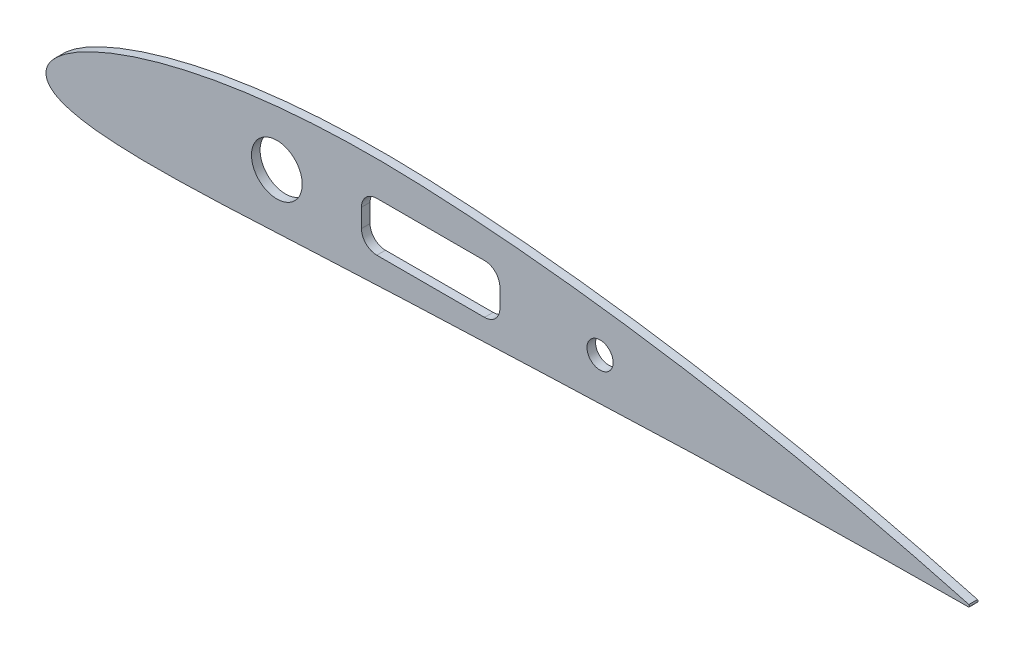
SolidWorks part; units mm, degrees
material "Фанера"
ref_plane "Front Plane" through (0, 0, 0) normal (0, 0, 1) x (1, 0, 0)
ref_plane "Top Plane" through (0, 0, 0) normal (0, 1, 0) x (1, 0, 0)
ref_plane "Right Plane" through (0, 0, 0) normal (1, 0, 0) x (0, 0, -1)
curve "Кривая3"
  spline degree 3 poles (0.0025, -0.1472, 0) (0.0289, -0.4455, 0) (0.0833, -1.0612, 0) (0.4227, -1.9666, 0) (0.9763, -2.8381, 0) (1.7565, -3.6471, 0) (2.7491, -4.3932, 0) (3.9671, -5.0829, 0) (5.4423, -5.7284, 0) (7.2357, -6.3386, 0) (9.4428, -6.9184, 0) (12.2026, -7.4661, 0) (15.6905, -7.9675, 0) (20.0737, -8.3915, 0) (25.4279, -8.6968, 0) (31.68, -8.852, 0) (38.6369, -8.8515, 0) (46.0774, -8.7137, 0) (53.8291, -8.468, 0) (61.7839, -8.1437, 0) (69.8772, -7.7668, 0) (78.0625, -7.3594, 0) (86.2929, -6.9408, 0) (94.5257, -6.5276, 0) (102.7326, -6.1331, 0) (110.9185, -5.7659, 0) (119.106, -5.4384, 0) (127.3169, -5.1339, 0) (135.5631, -4.8037, 0) (143.8373, -4.4678, 0) (152.1286, -4.1281, 0) (160.4179, -3.7904, 0) (168.6982, -3.4589, 0) (176.9664, -3.1367, 0) (185.2231, -2.8268, 0) (193.4701, -2.5312, 0) (201.709, -2.252, 0) (209.9419, -1.9904, 0) (218.1703, -1.7477, 0) (226.3959, -1.5245, 0) (234.62, -1.3213, 0) (242.8434, -1.1383, 0) (251.0655, -0.9754, 0) (259.2802, -0.8323, 0) (267.4637, -0.7084, 0) (275.5412, -0.6035, 0) (283.3048, -0.5178, 0) (290.3769, -0.4518, 0) (295.8708, -0.4074, 0) (298.9446, -0.3855, 0) (300, -0.378, 0) knots 0 0 0 0 0.002952 0.006093 0.009451 0.013105 0.017146 0.021696 0.026922 0.033053 0.040418 0.04948 0.060872 0.075263 0.09303 0.113914 0.137123 0.161847 0.187529 0.213845 0.240604 0.26768 0.294919 0.322129 0.349225 0.376201 0.403191 0.430285 0.457483 0.484832 0.512206 0.539574 0.566902 0.594186 0.62143 0.64864 0.675822 0.702982 0.730125 0.757257 0.784384 0.811507 0.838629 0.865737 0.892784 0.919595 0.94565 0.969591 0.989559 1 1 1 1
curve "Кривая4"
  spline degree 3 poles (300, 0.378, 0) (298.9868, 0.654, 0) (296.0642, 1.4502, 0) (290.8696, 2.83, 0) (284.2197, 4.5452, 0) (276.9359, 6.3576, 0) (269.3471, 8.1754, 0) (261.6367, 9.9499, 0) (253.8749, 11.6637, 0) (246.0869, 13.3108, 0) (238.2816, 14.8894, 0) (230.4628, 16.3984, 0) (222.6331, 17.8369, 0) (214.7944, 19.2041, 0) (206.9485, 20.4989, 0) (199.0972, 21.7198, 0) (191.2424, 22.8654, 0) (183.3862, 23.9339, 0) (175.5305, 24.9231, 0) (167.6776, 25.8308, 0) (159.8302, 26.6544, 0) (151.9904, 27.3909, 0) (144.1641, 28.0368, 0) (136.3543, 28.5896, 0) (128.5833, 29.0403, 0) (120.8893, 29.3981, 0) (113.2941, 29.624, 0) (105.7871, 29.6881, 0) (98.3389, 29.5906, 0) (90.9366, 29.3292, 0) (83.5844, 28.8983, 0) (76.2905, 28.2936, 0) (69.0662, 27.5099, 0) (61.9269, 26.5429, 0) (54.8933, 25.3879, 0) (47.995, 24.0424, 0) (41.2775, 22.5076, 0) (34.8125, 20.7931, 0) (28.711, 18.9262, 0) (23.1248, 16.9611, 0) (18.2149, 14.98, 0) (14.0886, 13.0747, 0) (10.7512, 11.3155, 0) (8.1131, 9.7303, 0) (6.0405, 8.3096, 0) (4.406, 7.0251, 0) (3.1105, 5.8456, 0) (2.0858, 4.7431, 0) (1.2838, 3.6971, 0) (0.686, 2.6899, 0) (0.2589, 1.7169, 0) (0.1227, 1.0599, 0) (0.0576, 0.7457, 0) knots 0 0 0 0 0.010162 0.029313 0.052012 0.076619 0.101948 0.127526 0.153184 0.178868 0.204558 0.230246 0.255926 0.281594 0.307246 0.332878 0.358485 0.384061 0.409603 0.435104 0.460559 0.485959 0.511303 0.536552 0.561723 0.586629 0.611085 0.635251 0.659272 0.683164 0.706922 0.730536 0.753983 0.777235 0.800246 0.822951 0.845237 0.866916 0.887662 0.906968 0.924203 0.938879 0.950932 0.960693 0.968647 0.975233 0.980795 0.985584 0.989782 0.993521 0.996902 1 1 1 1
sketch "Эскиз1" plane through (0, 0, 0) normal (0, 0, 1) x (1, 0, 0)
  line L0 (0.0576, 0.7457) -> (0, 0)
  line L1 (0, 0) -> (0.0025, -0.1472)
  line L2 (300.1566, 0) -> (300.1566, 178.5197) construction
  line L3 (0.0025, -0.1472) -> (0.0025, 211.821) construction
  line L4 (75.041, 185.5412) -> (75.041, -75.9832) construction
  line L5 (0, 0) -> (327.8081, 0) construction
  line L6 (180.0949, 113.6932) -> (180.0949, -104.9036) construction
  line L11 (75.041, 10.3156) -> (180.0949, 10.6624) construction
  line L12 (107.541, 2.4807) -> (142.541, 2.4807)
  line L13 (102.541, 7.4807) -> (102.541, 13.4807)
  line L14 (107.541, 18.4807) -> (142.541, 18.4807)
  line L15 (147.541, 7.4807) -> (147.541, 13.4807)
  line L16 (102.541, 2.4807) -> (147.541, 18.4807) construction
  line L17 (102.541, 18.4807) -> (147.541, 2.4807) construction
  arc A0 (300, 0.378) -> (300, -0.378) centre (299.622, 0) cw
  circle A1 centre (75.041, 10.3156) radius 8.25
  circle A6 centre (180.0949, 10.6624) radius 4.25
  arc A7 (142.541, 18.4807) -> (147.541, 13.4807) centre (142.541, 13.4807) cw
  arc A8 (142.541, 2.4807) -> (147.541, 7.4807) centre (142.541, 7.4807) ccw
  arc A9 (107.541, 2.4807) -> (102.541, 7.4807) centre (107.541, 7.4807) cw
  arc A10 (102.541, 13.4807) -> (107.541, 18.4807) centre (107.541, 13.4807) cw
  spline S0 degree 3 poles (-2950.6308, -536.1959) (67.2429, 38.3963) (-4.4143, 10.9383) (0.4227, -1.9666) (0.9763, -2.8381) (1.7565, -3.6471) (2.7491, -4.3932) (3.9671, -5.0829) (5.4423, -5.7284) (7.2357, -6.3386) (9.4428, -6.9184) (12.2026, -7.4661) (15.6905, -7.9675) (20.0737, -8.3915) (25.4279, -8.6968) (31.68, -8.852) (38.6369, -8.8515) (46.0774, -8.7137) (53.8291, -8.468) (61.7839, -8.1437) (69.8772, -7.7668) (78.0625, -7.3594) (86.2929, -6.9408) (94.5257, -6.5276) (102.7326, -6.1331) (110.9185, -5.7659) (119.106, -5.4384) (127.3169, -5.1339) (135.5631, -4.8037) (143.8373, -4.4678) (152.1286, -4.1281) (160.4179, -3.7904) (168.6982, -3.4589) (176.9664, -3.1367) (185.2231, -2.8268) (193.4701, -2.5312) (201.709, -2.252) (209.9419, -1.9904) (218.1703, -1.7477) (226.3959, -1.5245) (234.62, -1.3213) (242.8434, -1.1383) (253.799, -0.9213) (264.7237, -0.7439) (275.5412, -0.6035) (283.3048, -0.5178) (290.3769, -0.4518) (510.4851, 1.3263) (728.2809, -11.5299) (922.5933, 2892.7767) knots -0.125252 -0.125252 -0.125252 -0.125252 0.002952 0.006093 0.009451 0.013105 0.017146 0.021696 0.026922 0.033053 0.040418 0.04948 0.060872 0.075263 0.09303 0.113914 0.137123 0.161847 0.187529 0.213845 0.240604 0.26768 0.294919 0.322129 0.349225 0.376201 0.403191 0.430285 0.457483 0.484832 0.512206 0.539574 0.566902 0.594186 0.62143 0.64864 0.675822 0.702982 0.730125 0.757257 0.784384 0.811507 0.838629 0.892784 0.919595 0.94565 0.969591 0.989559 3.123159 3.123159 3.123159 3.123159 only from (0.0025, -0.1472) to (300, -0.378) construction
  spline S1 degree 3 poles (1406.1006, 2776.5975) (512.1301, -85.7233) (406.393, -27.8552) (290.8696, 2.83) (284.2197, 4.5452) (276.9359, 6.3576) (269.3471, 8.1754) (261.6367, 9.9499) (253.8749, 11.6637) (246.0869, 13.3108) (238.2816, 14.8894) (230.4628, 16.3984) (222.6331, 17.8369) (214.7944, 19.2041) (206.9485, 20.4989) (199.0972, 21.7198) (191.2424, 22.8654) (183.3862, 23.9339) (175.5305, 24.9231) (167.6776, 25.8308) (159.8302, 26.6544) (151.9904, 27.3909) (144.1641, 28.0368) (136.3543, 28.5896) (128.5833, 29.0403) (120.8893, 29.3981) (113.2941, 29.624) (105.7871, 29.6881) (98.3389, 29.5906) (90.9366, 29.3292) (83.5844, 28.8983) (76.2905, 28.2936) (69.0662, 27.5099) (61.9269, 26.5429) (54.8933, 25.3879) (47.995, 24.0424) (41.2775, 22.5076) (34.8125, 20.7931) (28.711, 18.9262) (23.1248, 16.9611) (18.2149, 14.98) (14.0886, 13.0747) (10.7512, 11.3155) (8.1131, 9.7303) (6.0405, 8.3096) (4.406, 7.0251) (3.1105, 5.8456) (2.0858, 4.7431) (1.2838, 3.6971) (0.686, 2.6899) (-5.6177, -11.6727) (57.5871, -46.3771) (-2885.6277, 816.5297) knots -1.104679 -1.104679 -1.104679 -1.104679 0.010162 0.029313 0.052012 0.076619 0.101948 0.127526 0.153184 0.178868 0.204558 0.230246 0.255926 0.281594 0.307246 0.332878 0.358485 0.384061 0.409603 0.435104 0.460559 0.485959 0.511303 0.536552 0.561723 0.586629 0.611085 0.635251 0.659272 0.683164 0.706922 0.730536 0.753983 0.777235 0.800246 0.822951 0.845237 0.866916 0.887662 0.906968 0.924203 0.938879 0.950932 0.960693 0.968647 0.975233 0.980795 0.985584 0.989782 0.993521 0.996902 1.140618 1.140618 1.140618 1.140618 only from (300, 0.378) to (0.0576, 0.7457) construction
  spline S2 degree 3 poles (0.0025, -0.1472) (0.0289, -0.4455) (0.0833, -1.0612) (0.4227, -1.9666) (0.9763, -2.8381) (1.7565, -3.6471) (2.7491, -4.3932) (3.9671, -5.0829) (5.4423, -5.7284) (7.2357, -6.3386) (9.4428, -6.9184) (12.2026, -7.4661) (15.6905, -7.9675) (20.0737, -8.3915) (25.4279, -8.6968) (31.68, -8.852) (38.6369, -8.8515) (46.0774, -8.7137) (53.8291, -8.468) (61.7839, -8.1437) (69.8772, -7.7668) (78.0625, -7.3594) (86.2929, -6.9408) (94.5257, -6.5276) (102.7326, -6.1331) (110.9185, -5.7659) (119.106, -5.4384) (127.3169, -5.1339) (135.5631, -4.8037) (143.8373, -4.4678) (152.1286, -4.1281) (160.4179, -3.7904) (168.6982, -3.4589) (176.9664, -3.1367) (185.2231, -2.8268) (193.4701, -2.5312) (201.709, -2.252) (209.9419, -1.9904) (218.1703, -1.7477) (226.3959, -1.5245) (234.62, -1.3213) (242.8434, -1.1383) (253.799, -0.9213) (264.7237, -0.7439) (275.5412, -0.6035) (283.3048, -0.5178) (290.3769, -0.4518) (295.8708, -0.4074) (298.9446, -0.3855) (300, -0.378) knots 0 0 0 0 0.002952 0.006093 0.009451 0.013105 0.017146 0.021696 0.026922 0.033053 0.040418 0.04948 0.060872 0.075263 0.09303 0.113914 0.137123 0.161847 0.187529 0.213845 0.240604 0.26768 0.294919 0.322129 0.349225 0.376201 0.403191 0.430285 0.457483 0.484832 0.512206 0.539574 0.566902 0.594186 0.62143 0.64864 0.675822 0.702982 0.730125 0.757257 0.784384 0.811507 0.838629 0.892784 0.919595 0.94565 0.969591 0.989559 1 1 1 1
  spline S3 degree 3 poles (300, 0.378) (298.9868, 0.654) (296.0642, 1.4502) (290.8696, 2.83) (284.2197, 4.5452) (276.9359, 6.3576) (269.3471, 8.1754) (261.6367, 9.9499) (253.8749, 11.6637) (246.0869, 13.3108) (238.2816, 14.8894) (230.4628, 16.3984) (222.6331, 17.8369) (214.7944, 19.2041) (206.9485, 20.4989) (199.0972, 21.7198) (191.2424, 22.8654) (183.3862, 23.9339) (175.5305, 24.9231) (167.6776, 25.8308) (159.8302, 26.6544) (151.9904, 27.3909) (144.1641, 28.0368) (136.3543, 28.5896) (128.5833, 29.0403) (120.8893, 29.3981) (113.2941, 29.624) (105.7871, 29.6881) (98.3389, 29.5906) (90.9366, 29.3292) (83.5844, 28.8983) (76.2905, 28.2936) (69.0662, 27.5099) (61.9269, 26.5429) (54.8933, 25.3879) (47.995, 24.0424) (41.2775, 22.5076) (34.8125, 20.7931) (28.711, 18.9262) (23.1248, 16.9611) (18.2149, 14.98) (14.0886, 13.0747) (10.7512, 11.3155) (8.1131, 9.7303) (6.0405, 8.3096) (4.406, 7.0251) (3.1105, 5.8456) (2.0858, 4.7431) (1.2838, 3.6971) (0.686, 2.6899) (0.2589, 1.7169) (0.1227, 1.0599) (0.0576, 0.7457) knots 0 0 0 0 0.010162 0.029313 0.052012 0.076619 0.101948 0.127526 0.153184 0.178868 0.204558 0.230246 0.255926 0.281594 0.307246 0.332878 0.358485 0.384061 0.409603 0.435104 0.460559 0.485959 0.511303 0.536552 0.561723 0.586629 0.611085 0.635251 0.659272 0.683164 0.706922 0.730536 0.753983 0.777235 0.800246 0.822951 0.845237 0.866916 0.887662 0.906968 0.924203 0.938879 0.950932 0.960693 0.968647 0.975233 0.980795 0.985584 0.989782 0.993521 0.996902 1 1 1 1
  point P12 (180.0949, 24.3448)
  point P14 (75.041, 28.1404)
  point P17 (75.041, -7.5092)
  point P20 (180.0949, -3.0199)
  point P21 (125.041, 10.4807)
  dimension "D1" = 0.5346
  dimension "D4" = 16.5
  dimension "D8" = 8.5
  dimension "D11" = 5
  dimension "D3" = 75.0385
  dimension "D5" = 35.6496
  dimension "D6" = 17.8248
  dimension "D2" = 180.0924
  dimension "D7" = 300.1541
  dimension "D9" = 27.3646
  dimension "D10" = 13.6823
  dimension "D12" = 45
  dimension "D13" = 16
  dimension "D14" = 50
extrude "Бобышка-Вытянуть1" add sketch "Эскиз1" along normal mid plane 2.8
equation "\"D3@Эскиз1\"=\"D7@Эскиз1\"/4"
equation "\"D6@Эскиз1\"=\"D5@Эскиз1\"/2"
equation "\"D2@Эскиз1\"=\"D7@Эскиз1\"*0.6"
equation "\"D10@Эскиз1\"=\"D9@Эскиз1\"/2"
